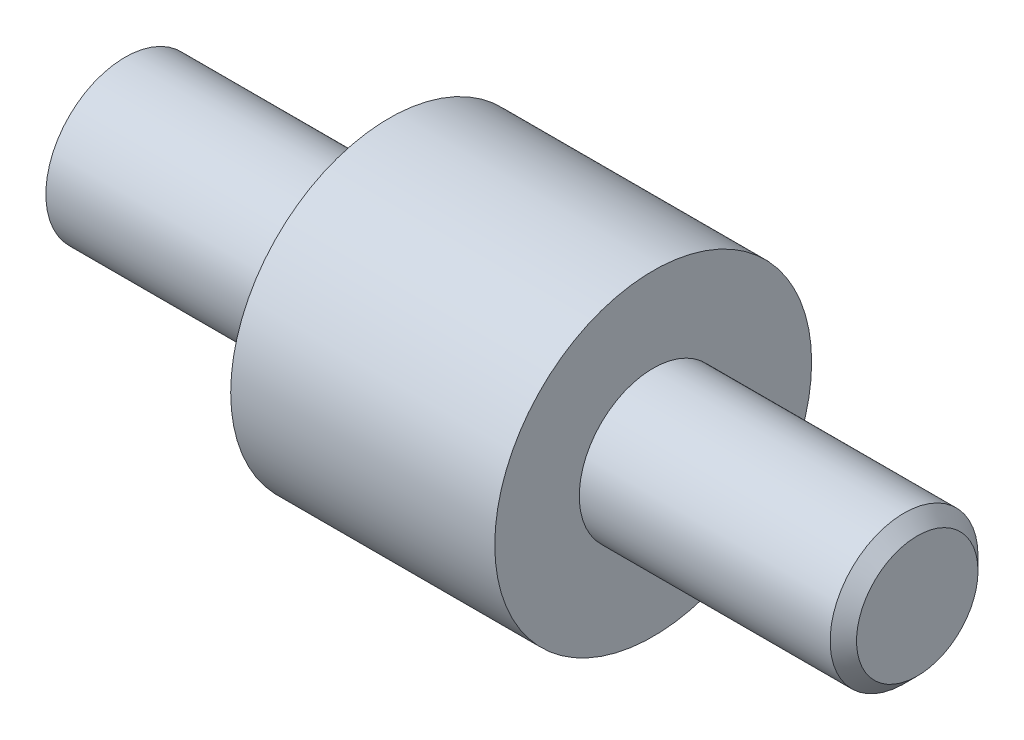
SolidWorks part; units mm, degrees
ref_plane "Plan de face" through (0, 0, 0) normal (0, 0, 1) x (1, 0, 0)
ref_plane "Plan de dessus" through (0, 0, 0) normal (0, 1, 0) x (1, 0, 0)
ref_plane "Plan de droite" through (0, 0, 0) normal (1, 0, 0) x (0, 0, -1)
sketch "Esquisse1" plane through (0, 0, 0) normal (0, 0, 1) x (1, 0, 0)
  line L0 (0, 0) -> (0, 1.5)
  line L1 (0, 1.5) -> (5, 1.5)
  line L2 (5, 1.5) -> (5, 3)
  line L3 (5, 3) -> (10, 3)
  line L4 (10, 3) -> (10, 1.4)
  line L5 (10, 1.4) -> (15, 1.4)
  line L6 (15, 1.4) -> (15, 0)
  line L7 (15, 0) -> (0, 0)
  dimension "D1" = 1.5
  dimension "D2" = 1.4
  dimension "D3" = 3
  dimension "D4" = 5
  dimension "D5" = 5
  dimension "D6" = 5
revolve "Révolution1" add sketch "Esquisse1" angle 360 about L7
chamfer "Chanfrein1" distance 0.25 angle 45 1 edges at (15, 0, -1.4)
